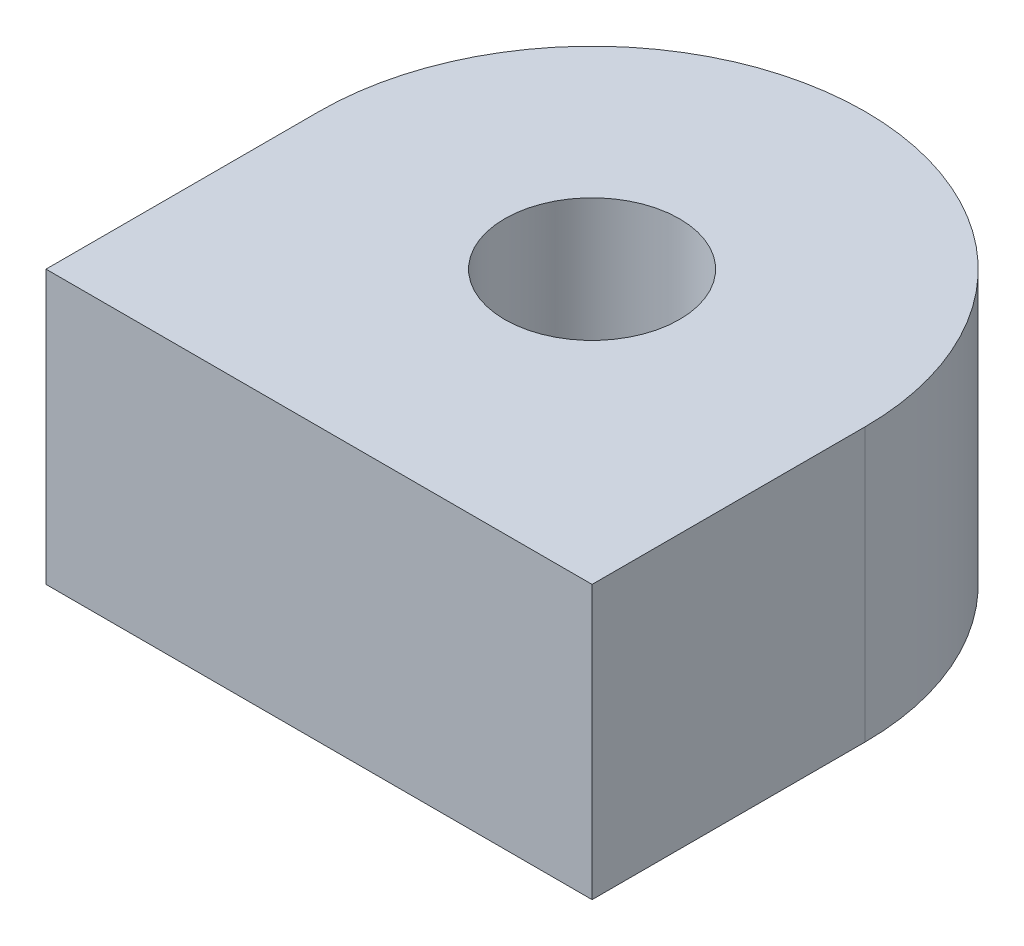
SolidWorks part; units mm, degrees
ref_plane "Front Plane" through (0, 0, 0) normal (0, 0, 1) x (1, 0, 0)
ref_plane "Top Plane" through (0, 0, 0) normal (0, 1, 0) x (1, 0, 0)
ref_plane "Right Plane" through (0, 0, 0) normal (1, 0, 0) x (0, 0, -1)
sketch "Sketch1" plane through (0, 0, 0) normal (0, 1, 0) x (1, 0, 0)
  line L0 (0, 0) -> (0, -10)
  line L1 (0, -10) -> (20, -10)
  line L2 (20, -10) -> (20, 0)
  arc A0 (0, 0) -> (20, 0) centre (10, 0) cw
  circle A1 centre (10, 0) radius 3.2
  point P9 (10, 0)
  dimension "D2" = 6.4
  dimension "D1" = 10
  dimension "D3" = 20
extrude "Boss-Extrude1" add sketch "Sketch1" against normal blind 10
